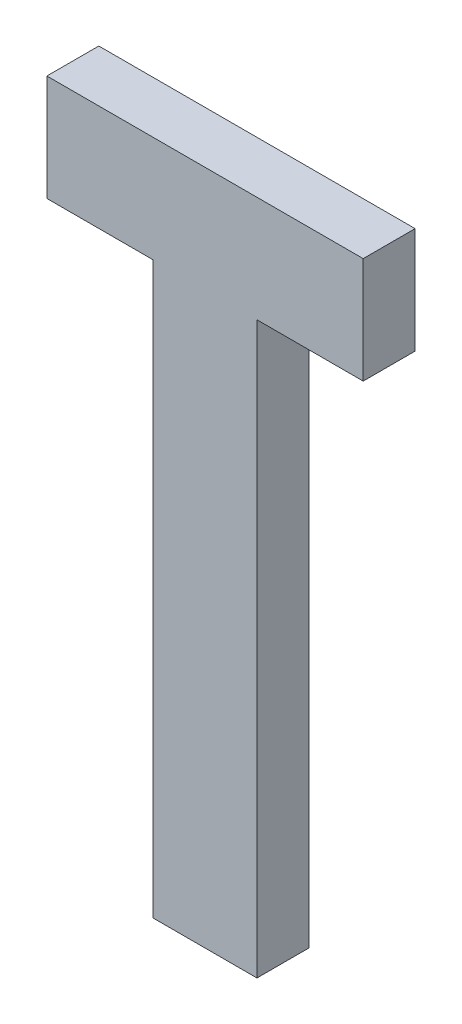
SolidWorks part; units mm, degrees
ref_plane "Front Plane" through (0, 0, 0) normal (0, 0, 1) x (1, 0, 0)
ref_plane "Top Plane" through (0, 0, 0) normal (0, 1, 0) x (1, 0, 0)
ref_plane "Right Plane" through (0, 0, 0) normal (1, 0, 0) x (0, 0, -1)
sketch "Sketch2" plane through (0, 0, 0) normal (0, 0, 1) x (1, 0, 0)
  line L0 (5, 24.8914) -> (15.2295, 24.8914)
  line L1 (-5, -30) -> (5, -30)
  line L2 (-5, -30) -> (-5, 24.8914)
  line L4 (5, -30) -> (5, 24.8914)
  line L5 (-5, -30) -> (0, 0) construction
  line L6 (0, 0) -> (5, -30) construction
  line L7 (-15.2295, 24.8914) -> (-5, 24.8914)
  line L8 (-15.2295, 24.8914) -> (-15.2295, 35.1086)
  line L9 (-15.2295, 35.1086) -> (15.2295, 35.1086)
  line L10 (15.2295, 24.8914) -> (15.2295, 35.1086)
  point P0 (0, 0)
  point P6 (0, 30)
  dimension "D1" = 10
extrude "Boss-Extrude2" add sketch "Sketch2" along normal blind 5
equation "\"D1@Boss-Extrude2\" = \"mat@V1.assembly\""
